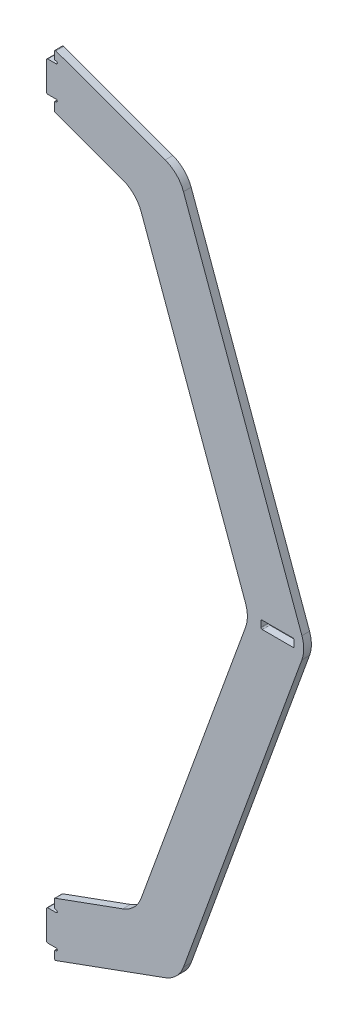
SolidWorks part; units mm, degrees
material "6061-T6 (SS)"
ref_plane "Front Plane" through (0, 0, 0) normal (0, 0, 1) x (1, 0, 0)
ref_plane "Top Plane" through (0, 0, 0) normal (0, 1, 0) x (1, 0, 0)
ref_plane "Right Plane" through (0, 0, 0) normal (1, 0, 0) x (0, 0, -1)
sketch "Sketch1" plane through (0, 0, 0) normal (0, 0, 1) x (1, 0, 0)
  line L0 (114.3, 158.75) -> (114.3, 146.05)
  line L1 (114.3, 146.05) -> (117.475, 146.05)
  line L2 (114.3, 158.75) -> (117.475, 158.75)
  line L3 (117.475, 158.75) -> (117.475, 163.576)
  line L4 (117.475, 146.05) -> (117.475, 141.224)
  line L5 (117.475, 141.224) -> (151.4771, 128.8483)
  line L6 (151.4771, 128.8483) -> (198.374, 0)
  line L7 (117.475, 163.576) -> (169.0357, 144.8095)
  line L8 (169.0357, 144.8095) -> (221.742, 0)
  line L9 (169.0357, -144.8095) -> (221.742, 0)
  line L10 (117.475, -163.576) -> (169.0357, -144.8095)
  line L11 (151.4771, -128.8483) -> (198.374, 0)
  line L12 (117.475, -141.224) -> (151.4771, -128.8483)
  line L13 (55, 0) -> (-55, 0) construction
  line L16 (117.475, -146.05) -> (117.475, -141.224)
  line L17 (117.475, -158.75) -> (117.475, -163.576)
  line L18 (114.3, -158.75) -> (117.475, -158.75)
  line L19 (114.3, -146.05) -> (117.475, -146.05)
  line L20 (114.3, -158.75) -> (114.3, -146.05)
  line L34 (216.916, -1.6764) -> (203.2, -1.6764)
  line L35 (216.916, -1.6764) -> (216.916, 1.6764)
  line L36 (216.916, 1.6764) -> (203.2, 1.6764)
  line L37 (203.2, -1.6764) -> (203.2, 1.6764)
  line L38 (216.916, -1.6764) -> (203.2, 1.6764) construction
  line L39 (216.916, 1.6764) -> (203.2, -1.6764) construction
  point P2 (114.3, 152.4)
  point P22 (210.058, 0)
  dimension "D1" = 114.3
  dimension "D2" = 3.175
  dimension "D3" = 12.7
  dimension "D4" = 152.4
  dimension "D5" = 4.826
  dimension "D6" = 20
  dimension "D7" = 20
  dimension "D8" = 4.826
  dimension "D10" = 4.826
  dimension "D15" = 3.3528
  dimension "D16" = 13.716
  dimension "D17" = 203.2
extrude "Boss-Extrude1" add sketch "Sketch1" along normal blind 3.175
fillet "Fillet1" radius 12.7 6 edges at (151.4771, -128.8483, 1.5875) (169.0357, -144.8095, 1.5875) (221.742, 0, 1.5875) (198.374, 0, 1.5875) (169.0357, 144.8095, 1.5875) (151.4771, 128.8483, 1.5875)
sketch "Sketch2" plane through (0, 0, 3.175) normal (0, 0, 1) x (1, 0, 0)
  line L0 (117.475, 146.05) -> (118.237, 146.05)
  line L1 (118.237, 145.034) -> (117.475, 145.034)
  line L2 (117.475, 146.05) -> (117.475, 141.224) construction
  line L3 (117.475, 158.75) -> (118.237, 158.75)
  line L4 (118.237, 159.766) -> (117.475, 159.766)
  line L5 (117.475, 163.576) -> (117.475, 158.75) construction
  line L6 (117.475, 158.75) -> (117.475, 159.766)
  line L7 (117.475, 145.034) -> (117.475, 146.05)
  line L8 (1.7463, 0) -> (-1.7463, 0) construction
  line L9 (117.475, -145.034) -> (117.475, -146.05)
  line L10 (117.475, -158.75) -> (117.475, -159.766)
  line L11 (118.237, -159.766) -> (117.475, -159.766)
  line L12 (117.475, -158.75) -> (118.237, -158.75)
  line L13 (118.237, -145.034) -> (117.475, -145.034)
  line L14 (117.475, -146.05) -> (118.237, -146.05)
  arc A0 (118.237, 146.05) -> (118.237, 145.034) centre (118.237, 145.542) cw
  arc A1 (118.237, 158.75) -> (118.237, 159.766) centre (118.237, 159.258) ccw
  arc A2 (118.237, -158.75) -> (118.237, -159.766) centre (118.237, -159.258) cw
  arc A3 (118.237, -146.05) -> (118.237, -145.034) centre (118.237, -145.542) ccw
  dimension "D2" = 0.508
  dimension "D1" = 0.762
extrude "Cut-Extrude1" cut sketch "Sketch2" against normal through all
fillet "Fillet2" radius 0.508 16 edges at (117.475, -141.224, 1.5875) (117.475, -145.034, 1.5875) (114.3, -146.05, 1.5875) (114.3, -158.75, 1.5875) (117.475, -159.766, 1.5875) (117.475, -163.576, 1.5875) (216.916, -1.6764, 1.5875) (216.916, 1.6764, 1.5875) (203.2, 1.6764, 1.5875) (203.2, -1.6764, 1.5875) (117.475, 141.224, 1.5875) (117.475, 145.034, 1.5875) (114.3, 146.05, 1.5875) (114.3, 158.75, 1.5875) (117.475, 159.766, 1.5875) (117.475, 163.576, 1.5875)
scale "Scale1" scale about centroid uniform scaling yes scale factor 0.35
